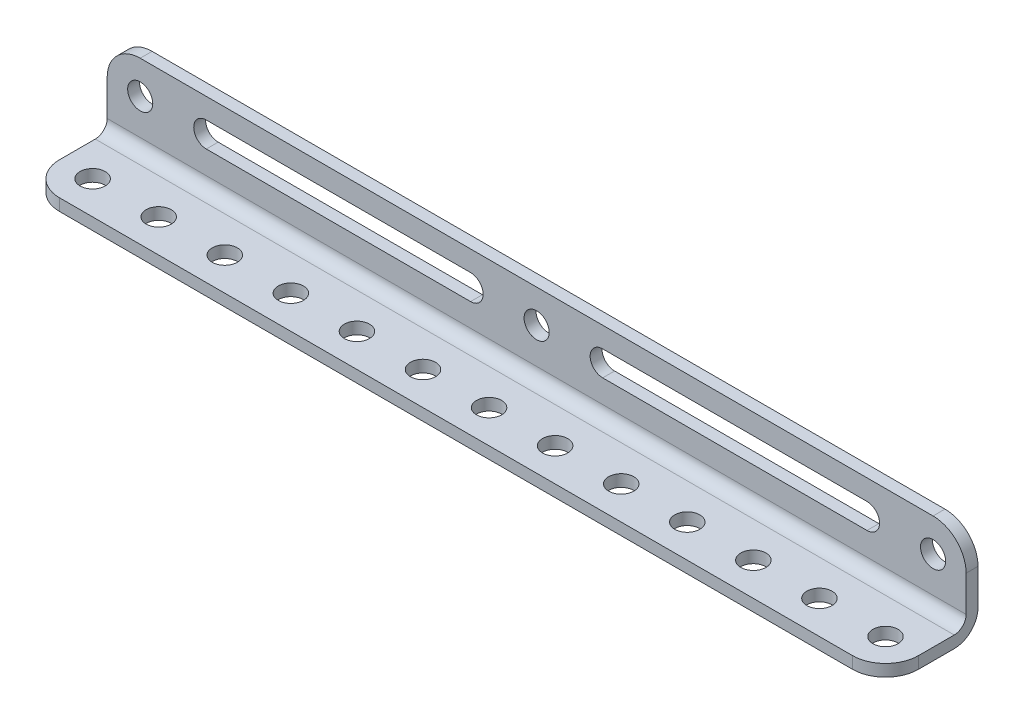
SolidWorks part; units mm, degrees
ref_plane "Front Plane" through (0, 0, 0) normal (0, 0, 1) x (1, 0, 0)
ref_plane "Top Plane" through (0, 0, 0) normal (0, 1, 0) x (1, 0, 0)
ref_plane "Right Plane" through (0, 0, 0) normal (1, 0, 0) x (0, 0, -1)
sketch "Sketch1" plane through (0, 0, 0) normal (1, 0, 0) x (0, 0, -1)
  line L0 (0, 0) -> (17.78, 0)
  line L1 (17.78, 0) -> (17.78, 17.78)
  dimension "D1" = 17.78
extrude "Extrude-Thin1" add sketch "Sketch1" along normal mid plane 165.1 thin thin type one direction reverse wall 2.286
sketch "Sketch2" plane through (0, 2.286, 0) normal (0, 1, 0) x (1, 0, 0)
  line L0 (82.55, 0) -> (-82.55, 0) construction
  circle A0 centre (-76.2, 6.35) radius 2.413
  dimension "D3" = 4.826
  dimension "D1" = 76.2
  dimension "D2" = 6.35
extrude "Cut-Extrude1" cut sketch "Sketch2" against normal through all
pattern_linear "LPattern1" count 13 spacing 12.7 along (1, 0, 0) of "Cut-Extrude1"
fillet "Fillet1" radius 6.35 4 edges at (82.55, 1.143, 0) (82.55, 17.78, -16.637) (-82.55, 1.143, 0) (-82.55, 17.78, -16.637)
sketch "Sketch3" plane through (0, 0, -15.494) normal (0, 0, 1) x (1, 0, 0)
  line L0 (76.2, 17.78) -> (-76.2, 17.78) construction
  circle A0 centre (-76.2, 11.43) radius 2.413
  dimension "D3" = 4.826
  dimension "D1" = 76.2
  dimension "D2" = 6.35
extrude "Cut-Extrude2" cut sketch "Sketch3" against normal through all
pattern_linear "LPattern2" count 3 spacing 76.2 along (1, 0, 0) of "Cut-Extrude2"
sketch "Sketch4" plane through (0, 0, -15.494) normal (0, 0, 1) x (1, 0, 0)
  line L0 (0, 0) -> (0, 11.43) construction
  line L2 (-63.5, 13.843) -> (-12.7, 13.843)
  line L4 (-63.5, 9.017) -> (-12.7, 9.017)
  line L6 (63.5, 13.843) -> (12.7, 13.843)
  line L8 (63.5, 9.017) -> (12.7, 9.017)
  arc A0 (-63.5, 13.843) -> (-63.5, 9.017) centre (-63.5, 11.43) ccw
  arc A1 (63.5, 13.843) -> (63.5, 9.017) centre (63.5, 11.43) cw
  arc A2 (-12.7, 13.843) -> (-12.7, 9.017) centre (-12.7, 11.43) cw
  arc A3 (12.7, 13.843) -> (12.7, 9.017) centre (12.7, 11.43) ccw
  circle A4 centre (0, 11.43) radius 2.413 construction
  dimension "D1" = 25.4
  dimension "D2" = 50.8
extrude "Cut-Extrude3" cut sketch "Sketch4" against normal through all
